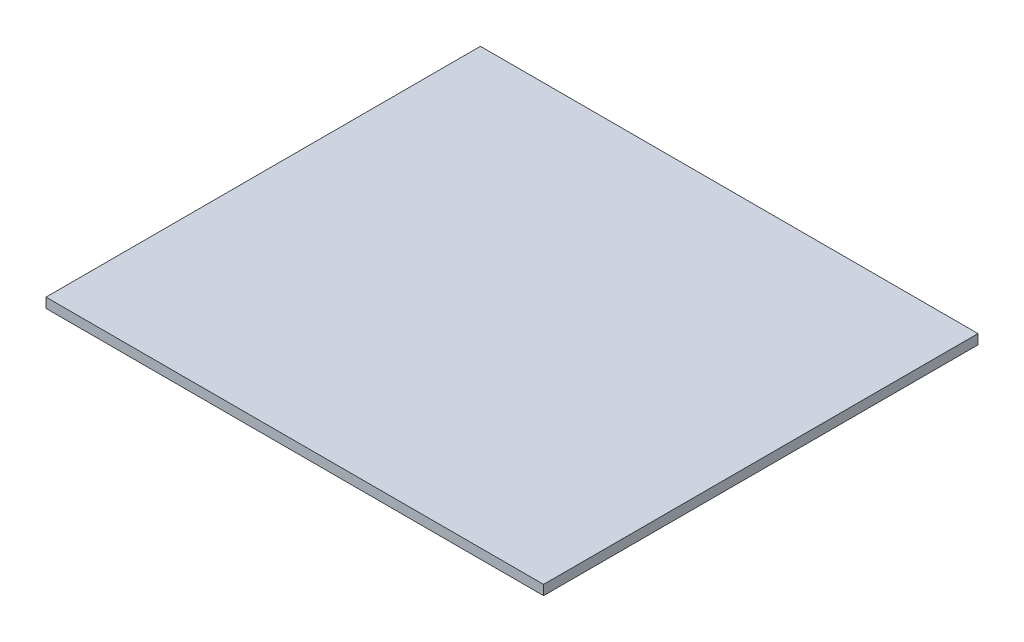
SolidWorks part; units mm, degrees
material "Oak"
ref_plane "Front Plane" through (0, 0, 0) normal (0, 0, 1) x (1, 0, 0)
ref_plane "Top Plane" through (0, 0, 0) normal (0, 1, 0) x (1, 0, 0)
ref_plane "Right Plane" through (0, 0, 0) normal (1, 0, 0) x (0, 0, -1)
sketch "Sketch1" plane through (0, 0, 0) normal (0, 1, 0) x (1, 0, 0)
  line L1 (0, 0) -> (838.2, 0)
  line L2 (0, 0) -> (0, 731.8375)
  line L3 (0, 731.8375) -> (838.2, 731.8375)
  line L4 (838.2, 0) -> (838.2, 731.8375)
  dimension "D1" = 731.8375
  dimension "D2" = 838.2
extrude "Boss-Extrude1" add sketch "Sketch1" along normal blind 19.05
chamfer "Chamfer1" distance 2.54 angle 45 4 edges at (419.1, 0, 0) (838.2, 0, -365.9187) (419.1, 0, -731.8375) (0, 0, -365.9187)
